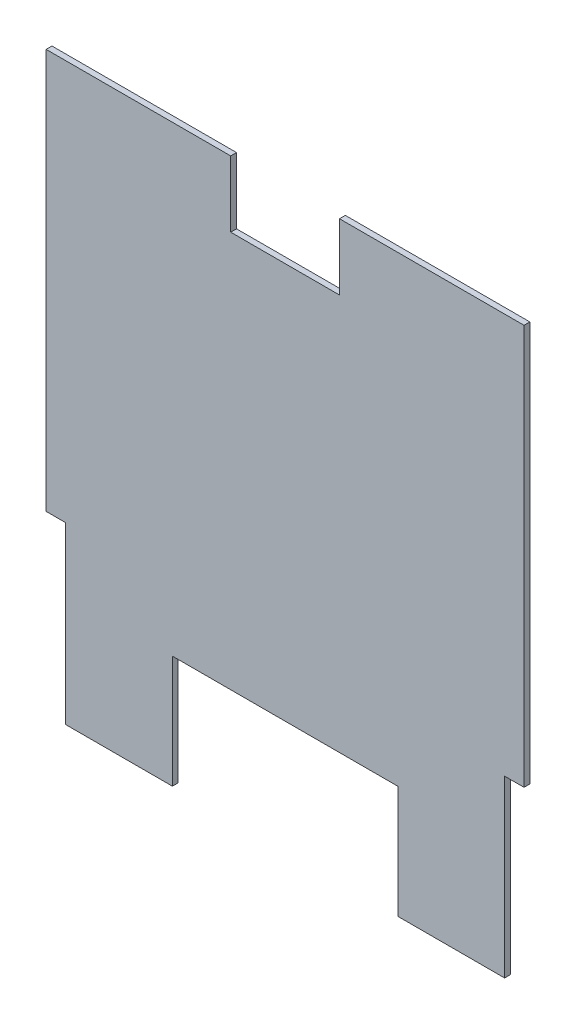
SolidWorks part; units mm, degrees
ref_plane "Front Plane" through (0, 0, 0) normal (0, 0, 1) x (1, 0, 0)
ref_plane "Top Plane" through (0, 0, 0) normal (0, 1, 0) x (1, 0, 0)
ref_plane "Right Plane" through (0, 0, 0) normal (1, 0, 0) x (0, 0, -1)
sketch "Sketch1" plane through (0, 0, 0) normal (0, 0, 1) x (1, 0, 0)
  line L0 (-92.075, -234.95) -> (-179.3875, -234.95)
  line L1 (179.3875, -234.95) -> (92.075, -234.95)
  line L2 (195.2625, -92.075) -> (195.2625, 234.95)
  line L3 (195.2625, 234.95) -> (44.45, 234.95)
  line L4 (-195.2625, -92.075) -> (-195.2625, 234.95)
  line L5 (0, 180.975) -> (0, -142.875) construction
  line L6 (-179.3875, -234.95) -> (-179.3875, -92.075)
  line L7 (-179.3875, -92.075) -> (-195.2625, -92.075)
  line L8 (92.075, -234.95) -> (92.075, -142.875)
  line L9 (92.075, -142.875) -> (-92.075, -142.875)
  line L10 (-92.075, -234.95) -> (-92.075, -142.875)
  line L11 (44.45, 180.975) -> (-44.45, 180.975)
  line L12 (-44.45, 180.975) -> (-44.45, 234.95)
  line L13 (44.45, 180.975) -> (44.45, 234.95)
  line L14 (-44.45, 234.95) -> (-195.2625, 234.95)
  line L15 (179.3875, -234.95) -> (179.3875, -92.075)
  line L16 (179.3875, -92.075) -> (195.2625, -92.075)
  point P0 (0, 0)
  point P6 (0, -234.95)
  dimension "D1" = 390.525
  dimension "D2" = 469.9
  dimension "D3" = 92.075
  dimension "D4" = 184.15
  dimension "D6" = 53.975
  dimension "D7" = 88.9
  dimension "D8" = 15.875
  dimension "D9" = 142.875
extrude "Boss-Extrude1" add sketch "Sketch1" along normal blind 4.7625
